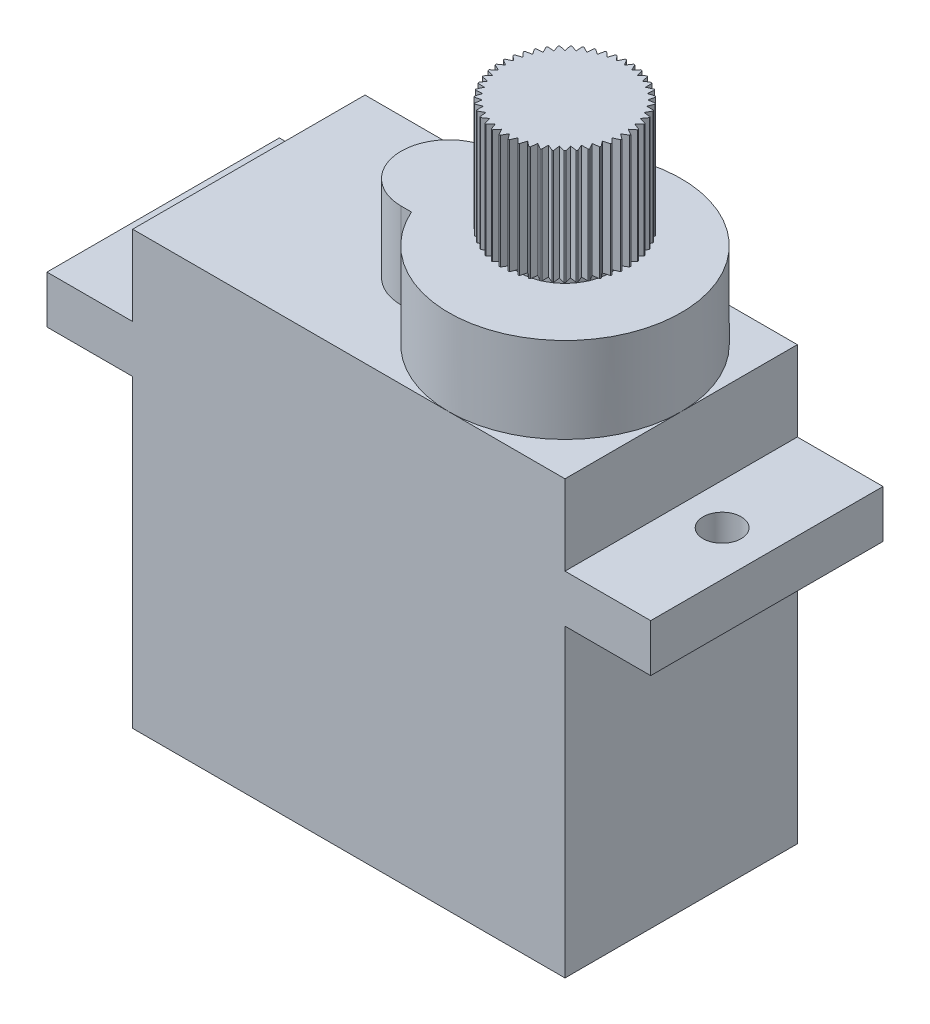
SolidWorks part; units mm, degrees
ref_plane "Front Plane" through (0, 0, 0) normal (0, 0, 1) x (1, 0, 0)
ref_plane "Top Plane" through (0, 0, 0) normal (0, 1, 0) x (1, 0, 0)
ref_plane "Right Plane" through (0, 0, 0) normal (1, 0, 0) x (0, 0, -1)
sketch "Sketch2" plane through (0, 0, 0) normal (0, 1, 0) x (1, 0, 0)
  line L1 (11.35, -6.1) -> (-11.35, -6.1)
  line L2 (11.35, -6.1) -> (11.35, 6.1)
  line L3 (11.35, 6.1) -> (-11.35, 6.1)
  line L4 (-11.35, -6.1) -> (-11.35, 6.1)
  line L5 (11.35, -6.1) -> (-11.35, 6.1) construction
  line L6 (11.35, 6.1) -> (-11.35, -6.1) construction
  point P0 (0, 0)
  dimension "D1" = 22.7
  dimension "D2" = 12.2
extrude "Boss-Extrude1" add sketch "Sketch2" along normal blind 6.7 and the other way blind 16
sketch "Sketch3" plane through (0, 0, 0) normal (0, 1, 0) x (1, 0, 0)
  line L0 (0, 6.1) -> (0, -6.1) construction
  line L1 (11.35, 6.1) -> (-11.35, 6.1) construction
  line L2 (-11.35, -6.1) -> (11.35, -6.1) construction
  line L3 (11.35, 6.1) -> (15.85, 6.1)
  line L4 (15.85, 6.1) -> (15.85, -6.1)
  line L5 (15.85, -6.1) -> (11.35, -6.1)
  line L6 (11.35, -6.1) -> (11.35, 6.1)
  line L7 (-15.85, -6.1) -> (-11.35, -6.1)
  line L8 (-15.85, 6.1) -> (-15.85, -6.1)
  line L9 (-11.35, 6.1) -> (-15.85, 6.1)
  line L10 (-11.35, -6.1) -> (-11.35, 6.1)
  line L11 (-15.85, 0) -> (15.85, 0) construction
  circle A0 centre (13.5, 0) radius 1
  circle A1 centre (-13.5, 0) radius 1
  dimension "D3" = 2
  dimension "D1" = 4.5
  dimension "D2" = 27
extrude "Boss-Extrude2" add sketch "Sketch3" along normal blind 2.5
sketch "Sketch4" plane through (0, 6.7, 0) normal (0, 1, 0) x (1, 0, 0)
  line L0 (-11.35, 0) -> (11.35, 0) construction
  line L1 (-11.35, 6.1) -> (-11.35, -6.1) construction
  line L2 (11.35, -6.1) -> (11.35, 6.1) construction
  line L3 (11.35, 6.1) -> (-11.35, 6.1) construction
  line L4 (-0.85, 0) -> (-0.85, 9.1702) construction
  line L5 (-0.85, 2.5) -> (-0.3142, 2.5)
  line L6 (-0.85, -2.5) -> (-0.3142, -2.5)
  arc A0 (-0.3142, -2.5) -> (-0.3142, 2.5) centre (5.25, 0) ccw
  arc A1 (-0.85, 2.5) -> (-0.85, -2.5) centre (-0.85, 0) ccw
  dimension "D1" = 5
extrude "Boss-Extrude3" add sketch "Sketch4" along normal blind 4.5
sketch "Sketch5" plane through (0, 11.2, 0) normal (0, 1, 0) x (1, 0, 0)
  circle A0 centre (5.25, 0) radius 2.425
  circle A1 centre (5.25, 0) radius 0.5
  point P1 (5.25, 0)
  dimension "D2" = 4.85
  dimension "D3" = 1
  dimension "D1" = 5.25
extrude "Boss-Extrude4" add sketch "Sketch5" along normal blind 2.7 separate body
sketch "Sketch6" plane through (0, 13.9, 0) normal (0, 1, 0) x (1, 0, 0)
  line L0 (5.25, 0) -> (5.25, 3) construction
  line L1 (5.3019, 3.0747) -> (5.5011, 3.3613)
  line L2 (5.5626, 3.3562) -> (5.7113, 3.0403)
  line L3 (5.25, 3) -> (5.75, 2.958) construction
  line L4 (5.5011, 3.3613) -> (5.5626, 3.3562)
  line L5 (5.7113, 3.0403) -> (5.9469, 3.2979)
  line L6 (5.9469, 3.2979) -> (6.0072, 3.2845)
  line L7 (6.0072, 3.2845) -> (6.1124, 2.9517)
  line L8 (6.1124, 2.9517) -> (6.3802, 3.1756)
  line L9 (6.3802, 3.1756) -> (6.4382, 3.1543)
  line L10 (6.4382, 3.1543) -> (6.4981, 2.8105)
  line L11 (6.4981, 2.8105) -> (6.7934, 2.9966)
  line L12 (6.7934, 2.9966) -> (6.848, 2.9678)
  line L13 (6.848, 2.9678) -> (6.8616, 2.619)
  line L14 (6.8616, 2.619) -> (7.179, 2.7641)
  line L15 (7.179, 2.7641) -> (7.2293, 2.7283)
  line L16 (7.2293, 2.7283) -> (7.1963, 2.3808)
  line L17 (7.1963, 2.3808) -> (7.5302, 2.4823)
  line L18 (7.5302, 2.4823) -> (7.5753, 2.4402)
  line L19 (7.5753, 2.4402) -> (7.4963, 2.1002)
  line L20 (7.4963, 2.1002) -> (7.8408, 2.1563)
  line L21 (7.8408, 2.1563) -> (7.8798, 2.1084)
  line L22 (7.8798, 2.1084) -> (7.7561, 1.7821)
  line L23 (7.7561, 1.7821) -> (8.105, 1.7917)
  line L24 (8.105, 1.7917) -> (8.1374, 1.7391)
  line L25 (8.1374, 1.7391) -> (7.9713, 1.4321)
  line L26 (7.9713, 1.4321) -> (8.3184, 1.3952)
  line L27 (8.3184, 1.3952) -> (8.3434, 1.3387)
  line L28 (8.3434, 1.3387) -> (8.1379, 1.0566)
  line L29 (8.1379, 1.0566) -> (8.477, 0.9738)
  line L30 (8.477, 0.9738) -> (8.4943, 0.9145)
  line L31 (8.4943, 0.9145) -> (8.253, 0.6623)
  line L32 (8.253, 0.6623) -> (8.578, 0.535)
  line L33 (8.578, 0.535) -> (8.5872, 0.4739)
  line L34 (8.5872, 0.4739) -> (8.3145, 0.2561)
  line L35 (8.3145, 0.2561) -> (8.6196, 0.0866)
  line L36 (8.6196, 0.0866) -> (8.6206, 0.0249)
  line L37 (8.6206, 0.0249) -> (8.3212, -0.1546)
  line L38 (8.3212, -0.1546) -> (8.6011, -0.3633)
  line L39 (8.6011, -0.3633) -> (8.5938, -0.4246)
  line L40 (8.5938, -0.4246) -> (8.2732, -0.5626)
  line L41 (8.2732, -0.5626) -> (8.5227, -0.8067)
  line L42 (8.5227, -0.8067) -> (8.5074, -0.8665)
  line L43 (8.5074, -0.8665) -> (8.1713, -0.9605)
  line L44 (8.1713, -0.9605) -> (8.386, -1.2357)
  line L45 (8.386, -1.2357) -> (8.3628, -1.2929)
  line L46 (8.3628, -1.2929) -> (8.0172, -1.3413)
  line L47 (8.0172, -1.3413) -> (8.1933, -1.6427)
  line L48 (8.1933, -1.6427) -> (8.1627, -1.6963)
  line L49 (8.1627, -1.6963) -> (7.8137, -1.6982)
  line L50 (7.8137, -1.6982) -> (7.9481, -2.0203)
  line L51 (7.9481, -2.0203) -> (7.9107, -2.0694)
  line L52 (7.9107, -2.0694) -> (7.5645, -2.0248)
  line L53 (7.5645, -2.0248) -> (7.6548, -2.3619)
  line L54 (7.6548, -2.3619) -> (7.6111, -2.4056)
  line L55 (7.6111, -2.4056) -> (7.274, -2.3152)
  line L56 (7.274, -2.3152) -> (7.3185, -2.6614)
  line L57 (7.3185, -2.6614) -> (7.2694, -2.6988)
  line L58 (7.2694, -2.6988) -> (6.9473, -2.5643)
  line L59 (6.9473, -2.5643) -> (6.9453, -2.9133)
  line L60 (6.9453, -2.9133) -> (6.8917, -2.9439)
  line L61 (6.8917, -2.9439) -> (6.5904, -2.7676)
  line L62 (6.5904, -2.7676) -> (6.5419, -3.1133)
  line L63 (6.5419, -3.1133) -> (6.4846, -3.1364)
  line L64 (6.4846, -3.1364) -> (6.2095, -2.9216)
  line L65 (6.2095, -2.9216) -> (6.1154, -3.2577)
  line L66 (6.1154, -3.2577) -> (6.0556, -3.273)
  line L67 (6.0556, -3.273) -> (5.8116, -3.0234)
  line L68 (5.8116, -3.0234) -> (5.6735, -3.344)
  line L69 (5.6735, -3.344) -> (5.6121, -3.3512)
  line L70 (5.6121, -3.3512) -> (5.4036, -3.0713)
  line L71 (5.4036, -3.0713) -> (5.224, -3.3706)
  line L72 (5.224, -3.3706) -> (5.1622, -3.3695)
  line L73 (5.1622, -3.3695) -> (4.9928, -3.0644)
  line L74 (4.9928, -3.0644) -> (4.775, -3.337)
  line L75 (4.775, -3.337) -> (4.7139, -3.3278)
  line L76 (4.7139, -3.3278) -> (4.5867, -3.0027)
  line L77 (4.5867, -3.0027) -> (4.3344, -3.2439)
  line L78 (4.3344, -3.2439) -> (4.2751, -3.2266)
  line L79 (4.2751, -3.2266) -> (4.1924, -2.8875)
  line L80 (4.1924, -2.8875) -> (3.9102, -3.093)
  line L81 (3.9102, -3.093) -> (3.8538, -3.0679)
  line L82 (3.8538, -3.0679) -> (3.8169, -2.7208)
  line L83 (3.8169, -2.7208) -> (3.5099, -2.8868)
  line L84 (3.5099, -2.8868) -> (3.4573, -2.8544)
  line L85 (3.4573, -2.8544) -> (3.4671, -2.5055)
  line L86 (3.4671, -2.5055) -> (3.1407, -2.6291)
  line L87 (3.1407, -2.6291) -> (3.0928, -2.59)
  line L88 (3.0928, -2.59) -> (3.149, -2.2455)
  line L89 (3.149, -2.2455) -> (2.8091, -2.3245)
  line L90 (2.8091, -2.3245) -> (2.7669, -2.2794)
  line L91 (2.7669, -2.2794) -> (2.8685, -1.9455)
  line L92 (2.8685, -1.9455) -> (2.521, -1.9784)
  line L93 (2.521, -1.9784) -> (2.4852, -1.9281)
  line L94 (2.4852, -1.9281) -> (2.6304, -1.6107)
  line L95 (2.6304, -1.6107) -> (2.2817, -1.597)
  line L96 (2.2817, -1.597) -> (2.2529, -1.5424)
  line L97 (2.2529, -1.5424) -> (2.4391, -1.2472)
  line L98 (2.4391, -1.2472) -> (2.0953, -1.1871)
  line L99 (2.0953, -1.1871) -> (2.0741, -1.1291)
  line L100 (2.0741, -1.1291) -> (2.298, -0.8614)
  line L101 (2.298, -0.8614) -> (1.9652, -0.7561)
  line L102 (1.9652, -0.7561) -> (1.9519, -0.6957)
  line L103 (1.9519, -0.6957) -> (2.2095, -0.4602)
  line L104 (2.2095, -0.4602) -> (1.8937, -0.3115)
  line L105 (1.8937, -0.3115) -> (1.8886, -0.2499)
  line L106 (1.8886, -0.2499) -> (2.1753, -0.0509)
  line L107 (2.1753, -0.0509) -> (1.8822, 0.1386)
  line L108 (1.8822, 0.1386) -> (1.8853, 0.2003)
  line L109 (1.8853, 0.2003) -> (2.1959, 0.3594)
  line L110 (2.1959, 0.3594) -> (1.9307, 0.5863)
  line L111 (1.9307, 0.5863) -> (1.942, 0.647)
  line L112 (1.942, 0.647) -> (2.2711, 0.7633)
  line L113 (2.2711, 0.7633) -> (2.0385, 1.0235)
  line L114 (2.0385, 1.0235) -> (2.0577, 1.0821)
  line L115 (2.0577, 1.0821) -> (2.3994, 1.1535)
  line L116 (2.3994, 1.1535) -> (2.2035, 1.4424)
  line L117 (2.2035, 1.4424) -> (2.2305, 1.498)
  line L118 (2.2305, 1.498) -> (2.5786, 1.5232)
  line L119 (2.5786, 1.5232) -> (2.423, 1.8356)
  line L120 (2.423, 1.8356) -> (2.4571, 1.8871)
  line L121 (2.4571, 1.8871) -> (2.8054, 1.8656)
  line L122 (2.8054, 1.8656) -> (2.6928, 2.196)
  line L123 (2.6928, 2.196) -> (2.7335, 2.2425)
  line L124 (2.7335, 2.2425) -> (3.0759, 2.1748)
  line L125 (3.0759, 2.1748) -> (3.0084, 2.5173)
  line L126 (3.0084, 2.5173) -> (3.0549, 2.5579)
  line L127 (3.0549, 2.5579) -> (3.3852, 2.4452)
  line L128 (3.3852, 2.4452) -> (3.3639, 2.7936)
  line L129 (3.3639, 2.7936) -> (3.4154, 2.8277)
  line L130 (3.4154, 2.8277) -> (3.7277, 2.6719)
  line L131 (3.7277, 2.6719) -> (3.7531, 3.02)
  line L132 (3.7531, 3.02) -> (3.8086, 3.047)
  line L133 (3.8086, 3.047) -> (4.0975, 2.851)
  line L134 (4.0975, 2.851) -> (4.1689, 3.1926)
  line L135 (4.1689, 3.1926) -> (4.2276, 3.2119)
  line L136 (4.2276, 3.2119) -> (4.4877, 2.9792)
  line L137 (4.4877, 2.9792) -> (4.6041, 3.3082)
  line L138 (4.6041, 3.3082) -> (4.6648, 3.3195)
  line L139 (4.6648, 3.3195) -> (4.8916, 3.0542)
  line L140 (4.8916, 3.0542) -> (5.0508, 3.3648)
  line L141 (5.0508, 3.3648) -> (5.1125, 3.3679)
  line L142 (5.1125, 3.3679) -> (5.3019, 3.0747)
  point P193 (5.25, 0)
  dimension "D2" = 0.5
  dimension "D3" = 60
  dimension "D4" = 0.44
  dimension "D5" = 0.3811
  dimension "D6" = 47
extrude "Boss-Extrude5" add sketch "Sketch6" along normal blind 4 and the other way blind 2
